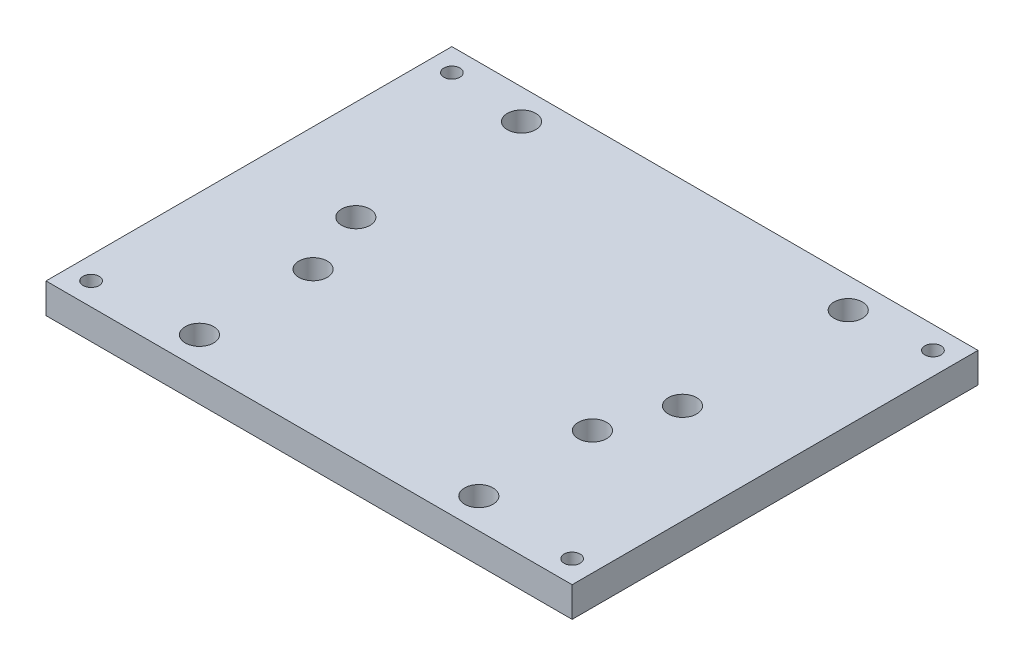
SolidWorks part; units mm, degrees
material "Polyurethane Foam Rigid"
ref_plane "Front Plane" through (0, 0, 0) normal (0, 0, 1) x (1, 0, 0)
ref_plane "Top Plane" through (0, 0, 0) normal (0, 1, 0) x (1, 0, 0)
ref_plane "Right Plane" through (0, 0, 0) normal (1, 0, 0) x (0, 0, -1)
sketch "Sketch1" plane through (0, 0, 0) normal (0, 1, 0) x (1, 0, 0)
  line L0 (-55.5625, 42.8625) -> (55.5625, 42.8625)
  line L1 (-50.8, -38.1) -> (50.8, -38.1) construction
  line L2 (-50.8, -38.1) -> (-50.8, 38.1) construction
  line L3 (-50.8, 38.1) -> (50.8, 38.1) construction
  line L4 (50.8, -38.1) -> (50.8, 38.1) construction
  line L5 (-50.8, -38.1) -> (50.8, 38.1) construction
  line L6 (-50.8, 38.1) -> (50.8, -38.1) construction
  line L7 (55.5625, -42.8625) -> (55.5625, 42.8625)
  line L8 (-55.5625, -42.8625) -> (55.5625, -42.8625)
  line L9 (-55.5625, -42.8625) -> (-55.5625, 42.8625)
  point P0 (0, 0)
  dimension "D1" = 101.6
  dimension "D2" = 76.2
  dimension "D3" = 4.7625
extrude "Boss-Extrude1" add sketch "Sketch1" along normal blind 6.35
hole_wizard "M3 Clearance Hole1" positions "3DSketch1" profile "Sketch2" hole size "M3" standard "ANSI Metric" end condition through all
sketch3d "3DSketch1"
  point P0 (-50.8, 0, 38.1)
  point P3 (50.8, 0, 38.1)
  point P6 (-50.8, 0, -38.1)
  point P9 (50.8, 0, -38.1)
sketch "Sketch2" plane through (-50.8, 0, 38.1) normal (1, 0, 0) x (0, 0, -1)
  line L0 (0, 0) -> (0, 6.35)
  line L1 (0, 6.35) -> (1.7, 6.35)
  line L2 (1.7, 6.35) -> (1.7, 0)
  line L5 (1.7, 0) -> (0, 0)
  line L11 (0, -6.35) -> (0, 107.95) construction
  dimension "Thru Hole Dia." = 3.4
  dimension "Thru Hole Depth" = 6.35
sketch "Sketch3" plane through (0, 6.35, 0) normal (0, 1, 0) x (1, 0, 0)
  line L0 (0, 19.0125) -> (0, -24.5125) construction
  line L1 (55.5625, 42.8625) -> (-55.5625, 42.8625) construction
  line L2 (-34.5, 1.5125) -> (34.5, 1.5125) construction
  line L3 (-34.5, 1.5125) -> (-34.5, 36.5125) construction
  line L4 (-34.5, 36.5125) -> (34.5, 36.5125) construction
  line L5 (34.5, 1.5125) -> (34.5, 36.5125) construction
  line L6 (-34.5, 1.5125) -> (34.5, 36.5125) construction
  line L7 (-34.5, 36.5125) -> (34.5, 1.5125) construction
  line L8 (-29.5, -12.5125) -> (29.5, -12.5125) construction
  line L9 (-29.5, -12.5125) -> (-29.5, -36.5125) construction
  line L10 (-29.5, -36.5125) -> (29.5, -36.5125) construction
  line L11 (29.5, -12.5125) -> (29.5, -36.5125) construction
  line L12 (-29.5, -12.5125) -> (29.5, -36.5125) construction
  line L13 (-29.5, -36.5125) -> (29.5, -12.5125) construction
  line L14 (-55.5625, -42.8625) -> (55.5625, -42.8625) construction
  circle A0 centre (-34.5, 36.5125) radius 3
  circle A1 centre (34.5, 36.5125) radius 3
  circle A2 centre (34.5, 1.5125) radius 3
  circle A3 centre (-34.5, 1.5125) radius 3
  circle A4 centre (-29.5, -12.5125) radius 3
  circle A5 centre (-29.5, -36.5125) radius 3
  circle A6 centre (29.5, -36.5125) radius 3
  circle A7 centre (29.5, -12.5125) radius 3
  dimension "D1" = 6
  dimension "D2" = 69
  dimension "D3" = 59
  dimension "D4" = 6.35
  dimension "D5" = 6.35
  dimension "D6" = 24
  dimension "D7" = 35
extrude "Cut-Extrude1" cut sketch "Sketch3" against normal through all
equation "\"D5@Sketch3\"=\"D4@Sketch3\""
